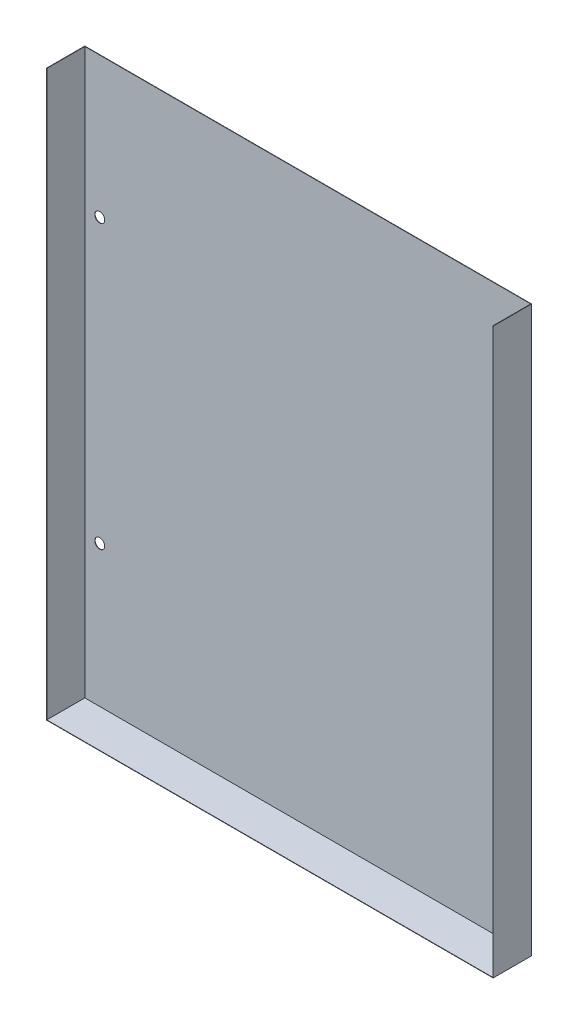
SolidWorks part; units mm, degrees
material "3003 Alloy"
ref_plane "Front Plane" through (0, 0, 0) normal (0, 0, 1) x (1, 0, 0)
ref_plane "Top Plane" through (0, 0, 0) normal (0, 1, 0) x (1, 0, 0)
ref_plane "Right Plane" through (0, 0, 0) normal (1, 0, 0) x (0, 0, -1)
sketch "Sketch1" plane through (0, 0, 0) normal (0, 0, 1) x (1, 0, 0)
  line L0 (-89.72, 113.5) -> (89.72, -113.5) construction
  line L1 (-89.72, -113.5) -> (89.72, -113.5)
  line L2 (-89.72, -113.5) -> (-89.72, 113.5)
  line L3 (-89.72, 113.5) -> (89.72, 113.5)
  line L4 (89.72, -113.5) -> (89.72, 113.5) construction
  line L5 (-83.72, 56.9786) -> (-83.72, -56.6738) construction
  line L6 (0, 113.5) -> (0, -113.5)
  circle A0 centre (-83.72, -56.6738) radius 2
  circle A1 centre (-83.72, 56.9786) radius 2
  dimension "D3" = 56.8262
  dimension "D5" = 6
  dimension "D6" = 4
  dimension "D7" = 4
  dimension "D1" = 179.44
  dimension "D2" = 227
  dimension "D4" = 170.4786
extrude "Heat Exchanger" add sketch "Sketch1" along normal blind 0.1524 contours L6 L3 L2 L1 A1 A0
sketch "Sketch3" plane through (0, 0, 0) normal (0, 0, 1) x (1, 0, 0)
  line L3 (0, -113.6524) -> (0, -113.5)
  line L5 (-89.8724, -113.6524) -> (0, -113.6524)
  line L6 (-89.8724, 113.5) -> (-89.8724, -113.6524)
  line L7 (-89.8724, -113.6524) -> (0, -113.6524)
  line L8 (-89.8724, 113.5) -> (-89.8724, -113.6524)
  line L9 (-89.8724, 113.5) -> (-89.72, 113.5)
  line L11 (-89.72, -113.5) -> (-89.72, 113.5) construction
  line L12 (-89.72, -113.5) -> (0, -113.5) construction
  line L13 (-89.72, -113.5) -> (-89.72, 113.5)
  line L14 (-89.72, -113.5) -> (0, -113.5)
  dimension "D1" = 0.1524
extrude "Convection Fin" add sketch "Sketch3" along normal blind 15.4517
mirror "Mirror1" about plane through (0, 0, 0) normal (1, 0, 0) of "Heat Exchanger", "Convection Fin"
